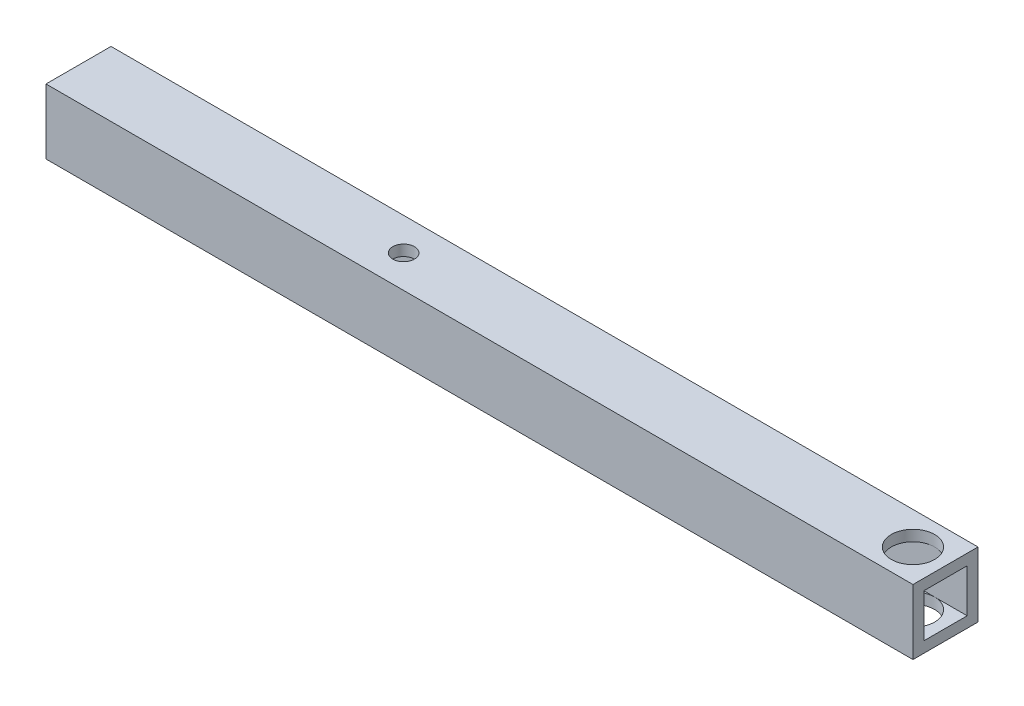
SolidWorks part; units mm, degrees
ref_plane "Front Plane" through (0, 0, 0) normal (0, 0, 1) x (1, 0, 0)
ref_plane "Top Plane" through (0, 0, 0) normal (0, 1, 0) x (1, 0, 0)
ref_plane "Right Plane" through (0, 0, 0) normal (1, 0, 0) x (0, 0, -1)
sketch "Sketch1" plane through (0, 0, 0) normal (1, 0, 0) x (0, 0, -1)
  line L1 (-7.5, -7.5) -> (7.5, -7.5)
  line L2 (-7.5, -7.5) -> (-7.5, 7.5)
  line L3 (-7.5, 7.5) -> (7.5, 7.5)
  line L4 (7.5, -7.5) -> (7.5, 7.5)
  line L5 (-7.5, -7.5) -> (7.5, 7.5) construction
  line L6 (-7.5, 7.5) -> (7.5, -7.5) construction
  line L7 (5, -5) -> (-5, -5)
  line L8 (5, -5) -> (5, 5)
  line L9 (5, 5) -> (-5, 5)
  line L10 (-5, -5) -> (-5, 5)
  line L11 (5, -5) -> (-5, 5) construction
  line L12 (5, 5) -> (-5, -5) construction
  point P0 (0, 0)
  point P6 (0, 0)
  dimension "D1" = 15
  dimension "D2" = 15
  dimension "D3" = 10
  dimension "D4" = 10
extrude "Boss-Extrude1" add sketch "Sketch1" along normal blind 200
sketch "Sketch2" plane through (0, 7.5, 0) normal (0, 1, 0) x (1, 0, 0)
  line L0 (200, 7.5) -> (200, -7.5) construction
  line L1 (200, -7.5) -> (0, -7.5) construction
  circle A0 centre (192.5, 0) radius 5
  dimension "D1" = 10
  dimension "D2" = 7.5
  dimension "D3" = 7.5
extrude "Cut-Extrude1" cut sketch "Sketch2" against normal through all
sketch "Sketch3" plane through (0, 7.5, 0) normal (0, 1, 0) x (1, 0, 0)
  line L0 (0, 7.5) -> (0, -7.5) construction
  line L1 (200, -7.5) -> (0, -7.5) construction
  circle A0 centre (75, 0) radius 2.5
  dimension "D1" = 5
  dimension "D2" = 75
  dimension "D3" = 7.5
extrude "Cut-Extrude2" cut sketch "Sketch3" against normal blind 100
